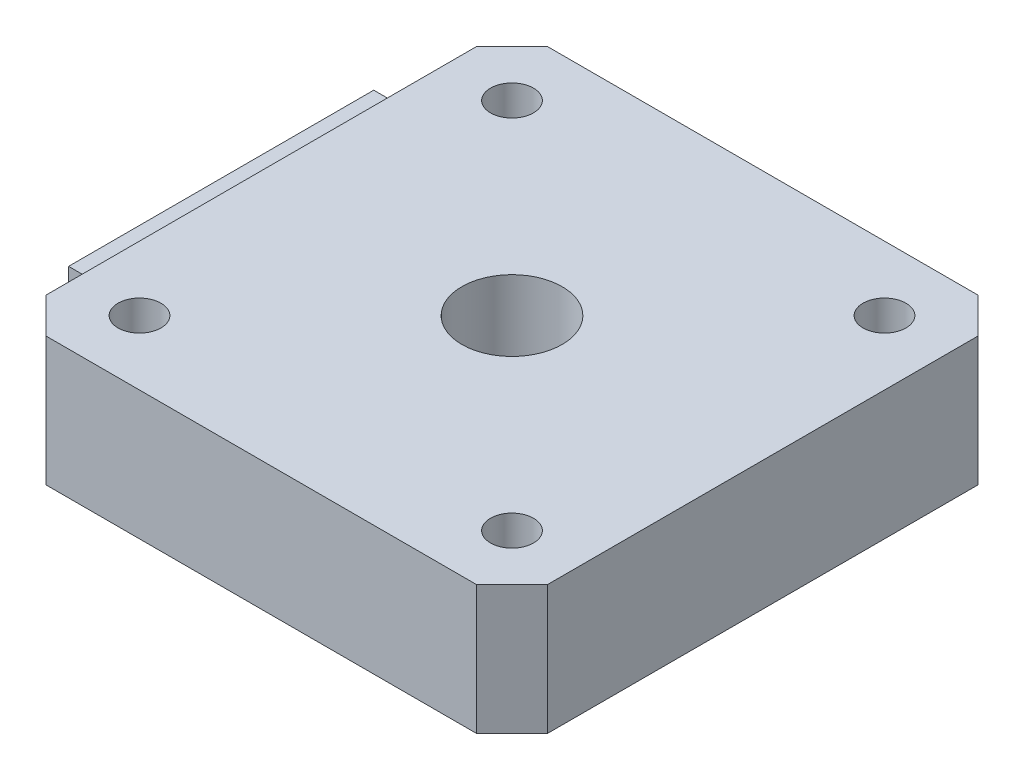
SolidWorks part; units mm, degrees
material "Aleación 1060"
ref_plane "Alzado" through (0, 0, 0) normal (0, 0, 1) x (1, 0, 0)
ref_plane "Planta" through (0, 0, 0) normal (0, 1, 0) x (1, 0, 0)
ref_plane "Vista lateral" through (0, 0, 0) normal (1, 0, 0) x (0, 0, -1)
sketch "Croquis1" plane through (0, 0, 0) normal (0, 1, 0) x (1, 0, 0)
  line L0 (0, 2.4731) -> (2.4731, 0)
  line L1 (2.4731, 0) -> (32.5269, 0)
  line L2 (32.5269, 0) -> (35, 2.4731)
  line L3 (35, 2.4731) -> (35, 32.5269)
  line L4 (35, 32.5269) -> (32.5269, 35)
  line L5 (32.5269, 35) -> (2.4731, 35)
  line L6 (2.4731, 35) -> (0, 32.5269)
  line L7 (0, 32.5269) -> (0, 2.4731)
  dimension "D1" = 35
  dimension "D2" = 35
  dimension "D3" = 46
  dimension "D4" = 46
  dimension "D5" = 45
extrude "Saliente-Extruir1" add sketch "Croquis1" along normal blind 9
sketch "Croquis2" plane through (0, 9, 0) normal (0, 1, 0) x (1, 0, 0)
  line L0 (17.5, 35) -> (17.5, 0) construction
  line L1 (32.5269, 35) -> (2.4731, 35) construction
  line L2 (2.4731, 0) -> (32.5269, 0) construction
  circle A0 centre (17.5, 17.5) radius 3.5
  dimension "D1" = 7
extrude "Cortar-Extruir1" cut sketch "Croquis2" against normal through all
sketch "Croquis3" plane through (0, 9, 0) normal (0, 1, 0) x (1, 0, 0)
  line L0 (4.5, 30.5) -> (30.5, 4.5) construction
  line L1 (4.5, 30.5) -> (30.5, 30.5) construction
  line L2 (4.5, 30.5) -> (4.5, 4.5) construction
  line L3 (4.5, 4.5) -> (30.5, 4.5) construction
  line L4 (30.5, 30.5) -> (30.5, 4.5) construction
  line L5 (4.5, 4.5) -> (30.5, 30.5) construction
  circle A0 centre (4.5, 30.5) radius 1.5
  circle A1 centre (30.5, 30.5) radius 1.5
  circle A2 centre (30.5, 4.5) radius 1.5
  circle A3 centre (4.5, 4.5) radius 1.5
  point P4 (17.5, 17.5)
  point P5 (17.5, 17.5)
  point P17 (17.5, 17.5)
  dimension "D3" = 3
  dimension "D1" = 26
  dimension "D2" = 26
  dimension "D4" = 4
extrude "Cortar-Extruir2" cut sketch "Croquis3" against normal through all
sketch "Sketch1" plane through (0, 0, 0) normal (-1, 0, 0) x (0, 0, 1)
  line L0 (-17.5, 0) -> (-17.5, 9) construction
  line L1 (-32.5269, 0) -> (-2.4731, 0) construction
  line L2 (-32.5269, 9) -> (-2.4731, 9) construction
  line L4 (-28.15, 0) -> (-6.85, 0)
  line L5 (-28.15, 0) -> (-28.15, 7.15)
  line L6 (-28.15, 7.15) -> (-6.85, 7.15)
  line L7 (-6.85, 0) -> (-6.85, 7.15)
  line L8 (-28.15, 0) -> (-6.85, 7.15) construction
  line L9 (-28.15, 7.15) -> (-6.85, 0) construction
  point P6 (-17.5, 3.575)
  dimension "D1" = 7.15
  dimension "D2" = 21.3
extrude "Boss-Extrude1" add sketch "Sketch1" along normal blind 2.8
sketch "Sketch2" plane through (-2.8, 0, 0) normal (-1, 0, 0) x (0, 0, 1)
  line L1 (-27.5, 0.575) -> (-7.5, 0.575)
  line L2 (-27.5, 0.575) -> (-27.5, 6.575)
  line L3 (-27.5, 6.575) -> (-7.5, 6.575)
  line L4 (-7.5, 0.575) -> (-7.5, 6.575)
  line L5 (-27.5, 0.575) -> (-7.5, 6.575) construction
  line L6 (-27.5, 6.575) -> (-7.5, 0.575) construction
  line L9 (-6.85, 7.15) -> (-28.15, 7.15) construction
  line L10 (-28.15, 7.15) -> (-28.15, 0) construction
  point P6 (-17.5, 3.575)
  point P7 (-17.5, 7.15)
  point P10 (-28.15, 3.575)
  dimension "D1" = 20
  dimension "D2" = 6
extrude "Cut-Extrude1" cut sketch "Sketch2" against normal blind 2.8
